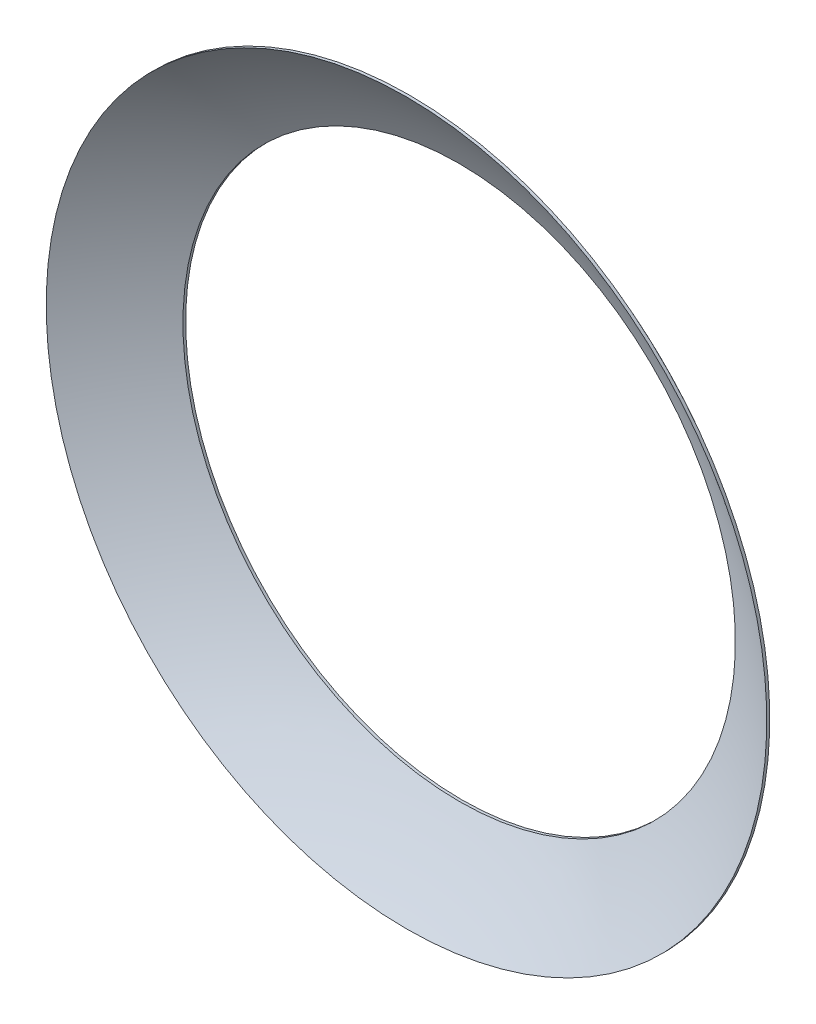
SolidWorks part; units mm, degrees
ref_plane "前视基准面" through (0, 0, 0) normal (0, 0, 1) x (1, 0, 0)
ref_plane "上视基准面" through (0, 0, 0) normal (0, 1, 0) x (1, 0, 0)
ref_plane "右视基准面" through (0, 0, 0) normal (1, 0, 0) x (0, 0, -1)
sketch "草图1" plane through (0, 0, 0) normal (0, 0, 1) x (1, 0, 0)
  line L0 (0, 175.7557) -> (0, -177.8882) construction
  line L1 (0, -125.2) -> (0, 125.2)
  arc A0 (0, 125.2) -> (0, -125.2) centre (0, 0) ccw
  dimension "D1" = 250.4
revolve "旋转1" add sketch "草图1" angle 180 about L0
shell "抽壳1" thickness 0.5
sketch "草图2" plane through (0, 0, 0) normal (0, 0, -1) x (1, 0, 0)
  line L0 (0, -75) -> (0, 75) construction
  circle A0 centre (0, 0) radius 75
  circle A1 centre (0, 0) radius 57.5
extrude "切除-拉伸1" cut sketch "草图2" along normal blind 323 flip side to cut
